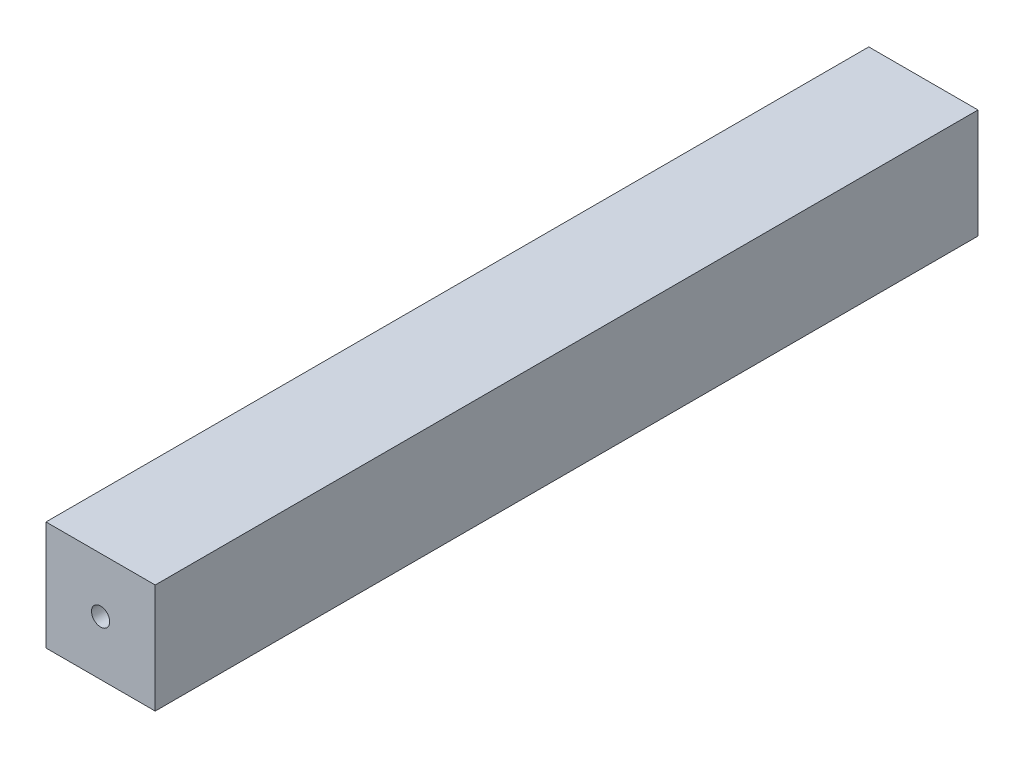
SolidWorks part; units mm, degrees
material "6061-T6 (SS)"
ref_plane "Plan de face" through (0, 0, 0) normal (0, 0, 1) x (1, 0, 0)
ref_plane "Plan de dessus" through (0, 0, 0) normal (0, 1, 0) x (1, 0, 0)
ref_plane "Plan de droite" through (0, 0, 0) normal (1, 0, 0) x (0, 0, -1)
sketch "Esquisse1" plane through (0, 0, 0) normal (0, 0, 1) x (1, 0, 0)
  line L0 (0, 15) -> (15, 0) construction
  line L1 (0, 0) -> (15, 0)
  line L2 (0, 0) -> (0, 15)
  line L3 (0, 15) -> (15, 15)
  line L4 (15, 0) -> (15, 15)
  circle A0 centre (7.5, 7.5) radius 1.25
  dimension "D2" = 2.5
  dimension "D1" = 15
extrude "Boss.-Extru.1" add sketch "Esquisse1" along normal blind 113
